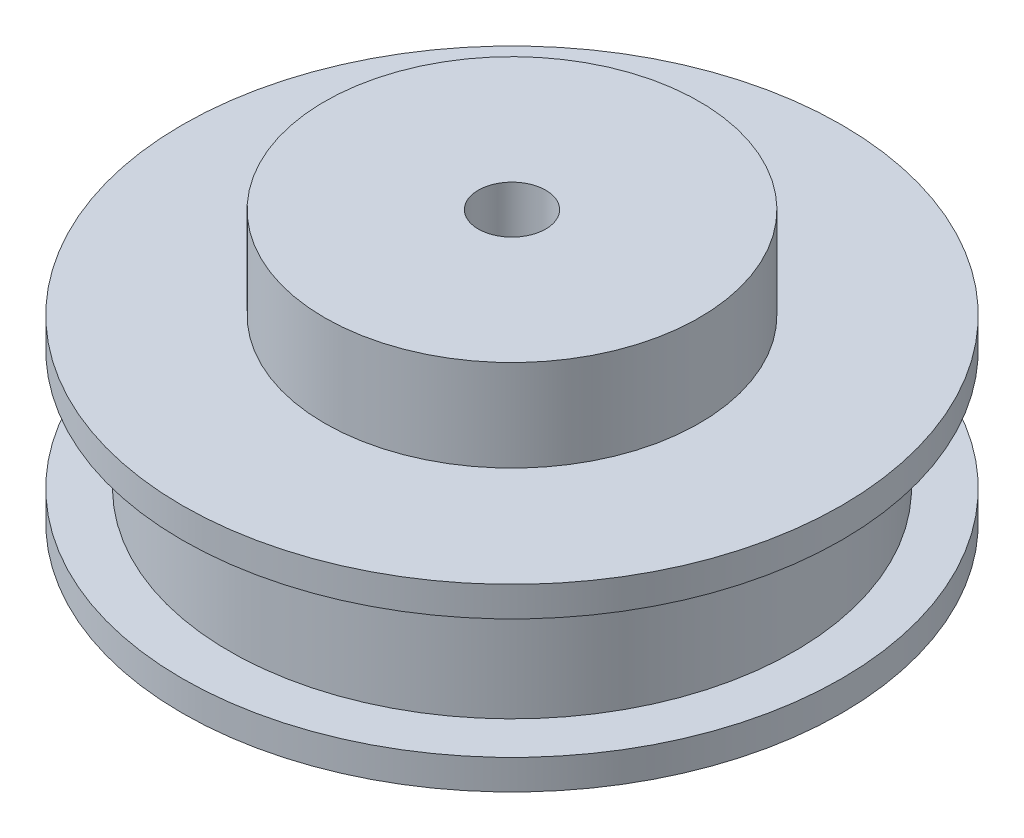
SolidWorks part; units mm, degrees
ref_plane "Front Plane" through (0, 0, 0) normal (0, 0, 1) x (1, 0, 0)
ref_plane "Top Plane" through (0, 0, 0) normal (0, 1, 0) x (1, 0, 0)
ref_plane "Right Plane" through (0, 0, 0) normal (1, 0, 0) x (0, 0, -1)
sketch "Sketch1" plane through (0, 0, 0) normal (0, 1, 0) x (1, 0, 0)
  circle A0 centre (0, 0) radius 22
  dimension "D1" = 44
extrude "Boss-Extrude1" add sketch "Sketch1" along normal blind 10
sketch "Sketch2" plane through (0, 10, 0) normal (0, 1, 0) x (1, 0, 0)
  circle A0 centre (0, 0) radius 12.5
  dimension "D1" = 25
extrude "Boss-Extrude2" add sketch "Sketch2" along normal blind 6.1
sketch "Sketch3" plane through (0, 0, 0) normal (0, -1, 0) x (1, 0, 0)
  circle A0 centre (0, 0) radius 18.85
  circle A2 centre (0, 0) radius 22
  circle A3 centre (0, 0) radius 22
  dimension "D1" = 37.7
  dimension "D2" = 0
extrude "Cut-Extrude2" cut sketch "Sketch3" against normal blind 8 contours A3 | A0
sketch "Sketch5" plane through (0, 0, 0) normal (0, -1, 0) x (1, 0, 0)
  circle A1 centre (0, 0) radius 22
  circle A2 centre (0, 0) radius 22
  dimension "D1" = 0
extrude "Boss-Extrude3" add sketch "Sketch5" along normal blind 2 contours A2
sketch "Sketch6" plane through (0, -2, 0) normal (0, -1, 0) x (1, 0, 0)
  circle A0 centre (0, 0) radius 2.25
  dimension "D1" = 4.5
extrude "Cut-Extrude3" cut sketch "Sketch6" against normal blind 28
